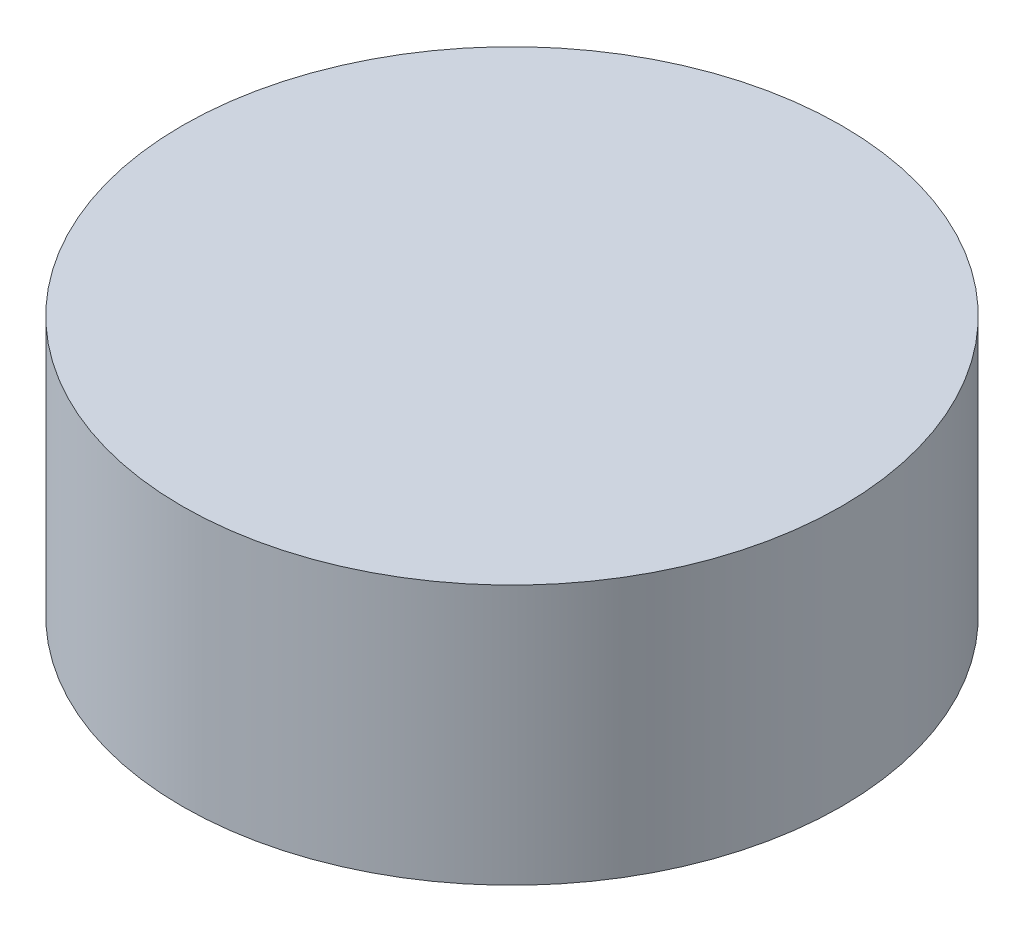
SolidWorks part; units mm, degrees
ref_plane "Front" through (0, 0, 0) normal (0, 0, 1) x (1, 0, 0)
ref_plane "Top" through (0, 0, 0) normal (0, 1, 0) x (1, 0, 0)
ref_plane "Right" through (0, 0, 0) normal (1, 0, 0) x (0, 0, -1)
sketch "Sketch1" plane through (0, 0, 0) normal (0, 1, 0) x (1, 0, 0)
  circle A0 centre (0, 0) radius 52
  dimension "D1" = 104
extrude "Boss-Extrude1" add sketch "Sketch1" along normal blind 41
